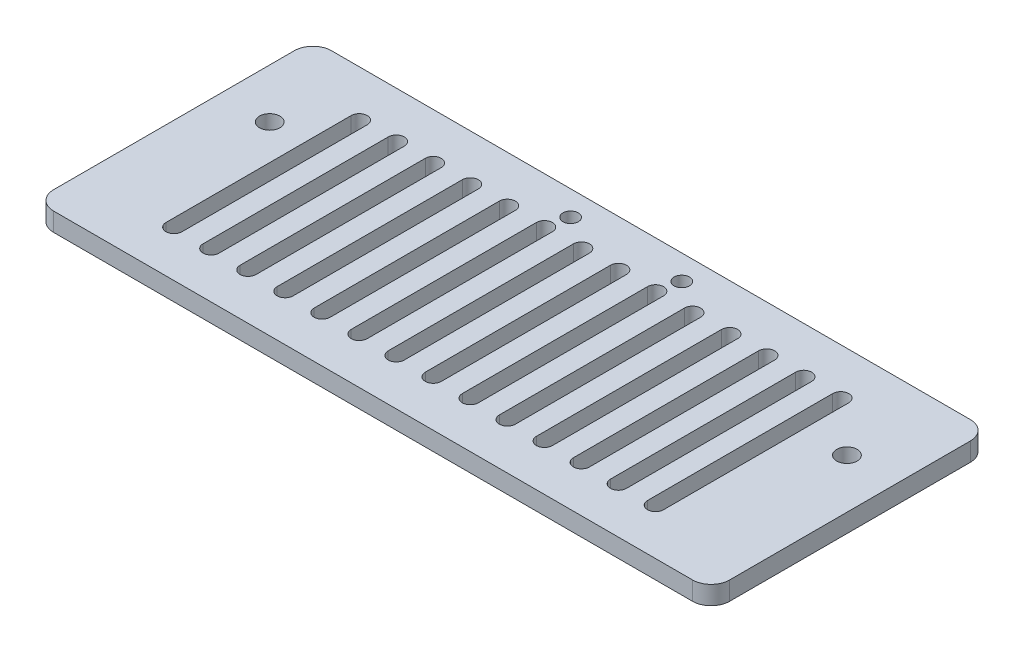
SolidWorks part; units mm, degrees
material "A-玻璃纤维"
ref_plane "前视基准面" through (0, 0, 0) normal (0, 0, 1) x (1, 0, 0)
ref_plane "上视基准面" through (0, 0, 0) normal (0, 1, 0) x (1, 0, 0)
ref_plane "右视基准面" through (0, 0, 0) normal (1, 0, 0) x (0, 0, -1)
sketch "草图1" plane through (0, 0, 0) normal (0, 1, 0) x (1, 0, 0)
  line L1 (-54.75, 22.5) -> (54.75, 22.5)
  line L2 (-54.75, 22.5) -> (-54.75, -22.5)
  line L3 (-54.75, -22.5) -> (54.75, -22.5)
  line L4 (54.75, 22.5) -> (54.75, -22.5)
  line L5 (-54.75, 22.5) -> (54.75, -22.5) construction
  line L6 (-54.75, -22.5) -> (54.75, 22.5) construction
  point P0 (0, 0)
  dimension "D1" = 109.5
  dimension "D2" = 45
extrude "凸台-拉伸1" add sketch "草图1" along normal blind 3
sketch "草图2" plane through (0, 3, 0) normal (0, 1, 0) x (1, 0, 0)
  line L0 (0, 0) -> (0, 22.5) construction
  line L1 (54.75, 22.5) -> (-54.75, 22.5) construction
  line L2 (0, 18.5) -> (9, 18.5) construction
  circle A0 centre (9, 18.5) radius 1.25
  circle A1 centre (-9, 18.5) radius 1.25
  dimension "D2" = 2.5
  dimension "D1" = 9
  dimension "D3" = 4
extrude "切除-拉伸1" cut sketch "草图2" against normal blind 10
sketch "草图3" plane through (0, 3, 0) normal (0, 1, 0) x (1, 0, 0)
  line L0 (-46.75, 22.5) -> (-46.75, 7.5) construction
  line L1 (54.75, 22.5) -> (-54.75, 22.5) construction
  line L2 (-54.75, 22.5) -> (-54.75, -22.5) construction
  line L3 (0, 0) -> (0, 25.2474) construction
  line L4 (46.75, 22.5) -> (46.75, 7.5) construction
  circle A0 centre (-46.75, 7.5) radius 1.65
  circle A1 centre (46.75, 7.5) radius 1.65
  dimension "D1" = 3.3
  dimension "D2" = 8
  dimension "D3" = 15
extrude "切除-拉伸2" cut sketch "草图3" against normal blind 10
fillet "圆角1" radius 3 4 edges at (54.75, 1.5, 22.5) (-54.75, 1.5, -22.5) (54.75, 1.5, -22.5) (-54.75, 1.5, 22.5)
sketch "草图4" plane through (0, 3, 0) normal (0, 1, 0) x (1, 0, 0)
  line L0 (-54.75, 0) -> (54.75, 0) construction
  line L1 (-54.75, 19.5) -> (-54.75, -19.5) construction
  line L2 (54.75, -19.5) -> (54.75, 19.5) construction
  line L3 (-39.75, 15) -> (-39.75, -15) construction
  line L4 (-38.45, 15) -> (-38.45, -15)
  line L5 (-41.05, 15) -> (-41.05, -15)
  line L6 (-33.75, 15) -> (-33.75, -15) construction
  line L7 (-32.45, 15) -> (-32.45, -15)
  line L8 (-35.05, 15) -> (-35.05, -15)
  line L9 (-27.75, 15) -> (-27.75, -15) construction
  line L10 (-26.45, 15) -> (-26.45, -15)
  line L11 (-29.05, 15) -> (-29.05, -15)
  line L12 (-21.75, 15) -> (-21.75, -15) construction
  line L13 (-20.45, 15) -> (-20.45, -15)
  line L14 (-23.05, 15) -> (-23.05, -15)
  line L15 (-15.75, 15) -> (-15.75, -15) construction
  line L16 (-14.45, 15) -> (-14.45, -15)
  line L17 (-17.05, 15) -> (-17.05, -15)
  line L18 (-9.75, 15) -> (-9.75, -15) construction
  line L19 (-8.45, 15) -> (-8.45, -15)
  line L20 (-11.05, 15) -> (-11.05, -15)
  line L21 (-3.75, 15) -> (-3.75, -15) construction
  line L22 (-2.45, 15) -> (-2.45, -15)
  line L23 (-5.05, 15) -> (-5.05, -15)
  line L24 (2.25, 15) -> (2.25, -15) construction
  line L25 (3.55, 15) -> (3.55, -15)
  line L26 (0.95, 15) -> (0.95, -15)
  line L27 (8.25, 15) -> (8.25, -15) construction
  line L28 (9.55, 15) -> (9.55, -15)
  line L29 (6.95, 15) -> (6.95, -15)
  line L30 (14.25, 15) -> (14.25, -15) construction
  line L31 (15.55, 15) -> (15.55, -15)
  line L32 (12.95, 15) -> (12.95, -15)
  line L33 (20.25, 15) -> (20.25, -15) construction
  line L34 (21.55, 15) -> (21.55, -15)
  line L35 (18.95, 15) -> (18.95, -15)
  line L36 (26.25, 15) -> (26.25, -15) construction
  line L37 (27.55, 15) -> (27.55, -15)
  line L38 (24.95, 15) -> (24.95, -15)
  line L39 (32.25, 15) -> (32.25, -15) construction
  line L40 (33.55, 15) -> (33.55, -15)
  line L41 (30.95, 15) -> (30.95, -15)
  line L42 (38.25, 15) -> (38.25, -15) construction
  line L43 (39.55, 15) -> (39.55, -15)
  line L44 (36.95, 15) -> (36.95, -15)
  arc A0 (-38.45, 15) -> (-41.05, 15) centre (-39.75, 15) ccw
  arc A1 (-41.05, -15) -> (-38.45, -15) centre (-39.75, -15) ccw
  arc A2 (-32.45, 15) -> (-35.05, 15) centre (-33.75, 15) ccw
  arc A3 (-35.05, -15) -> (-32.45, -15) centre (-33.75, -15) ccw
  arc A4 (-26.45, 15) -> (-29.05, 15) centre (-27.75, 15) ccw
  arc A5 (-29.05, -15) -> (-26.45, -15) centre (-27.75, -15) ccw
  arc A6 (-20.45, 15) -> (-23.05, 15) centre (-21.75, 15) ccw
  arc A7 (-23.05, -15) -> (-20.45, -15) centre (-21.75, -15) ccw
  arc A8 (-14.45, 15) -> (-17.05, 15) centre (-15.75, 15) ccw
  arc A9 (-17.05, -15) -> (-14.45, -15) centre (-15.75, -15) ccw
  arc A10 (-8.45, 15) -> (-11.05, 15) centre (-9.75, 15) ccw
  arc A11 (-11.05, -15) -> (-8.45, -15) centre (-9.75, -15) ccw
  arc A12 (-2.45, 15) -> (-5.05, 15) centre (-3.75, 15) ccw
  arc A13 (-5.05, -15) -> (-2.45, -15) centre (-3.75, -15) ccw
  arc A14 (3.55, 15) -> (0.95, 15) centre (2.25, 15) ccw
  arc A15 (0.95, -15) -> (3.55, -15) centre (2.25, -15) ccw
  arc A16 (9.55, 15) -> (6.95, 15) centre (8.25, 15) ccw
  arc A17 (6.95, -15) -> (9.55, -15) centre (8.25, -15) ccw
  arc A18 (15.55, 15) -> (12.95, 15) centre (14.25, 15) ccw
  arc A19 (12.95, -15) -> (15.55, -15) centre (14.25, -15) ccw
  arc A20 (21.55, 15) -> (18.95, 15) centre (20.25, 15) ccw
  arc A21 (18.95, -15) -> (21.55, -15) centre (20.25, -15) ccw
  arc A22 (27.55, 15) -> (24.95, 15) centre (26.25, 15) ccw
  arc A23 (24.95, -15) -> (27.55, -15) centre (26.25, -15) ccw
  arc A24 (33.55, 15) -> (30.95, 15) centre (32.25, 15) ccw
  arc A25 (30.95, -15) -> (33.55, -15) centre (32.25, -15) ccw
  arc A26 (39.55, 15) -> (36.95, 15) centre (38.25, 15) ccw
  arc A27 (36.95, -15) -> (39.55, -15) centre (38.25, -15) ccw
  point P8 (-39.75, 0)
  point P16 (-33.75, 0)
  point P23 (-27.75, 0)
  point P30 (-21.75, 0)
  point P37 (-15.75, 0)
  point P44 (-9.75, 0)
  point P51 (-3.75, 0)
  point P58 (2.25, 0)
  point P65 (8.25, 0)
  point P72 (14.25, 0)
  point P79 (20.25, 0)
  point P86 (26.25, 0)
  point P93 (32.25, 0)
  point P100 (38.25, 0)
  dimension "D1" = 1.3
  dimension "D2" = 15
  dimension "D3" = 30
  dimension "D5" = 6
  dimension "D4" = 14
extrude "切除-拉伸3" cut sketch "草图4" against normal through all
